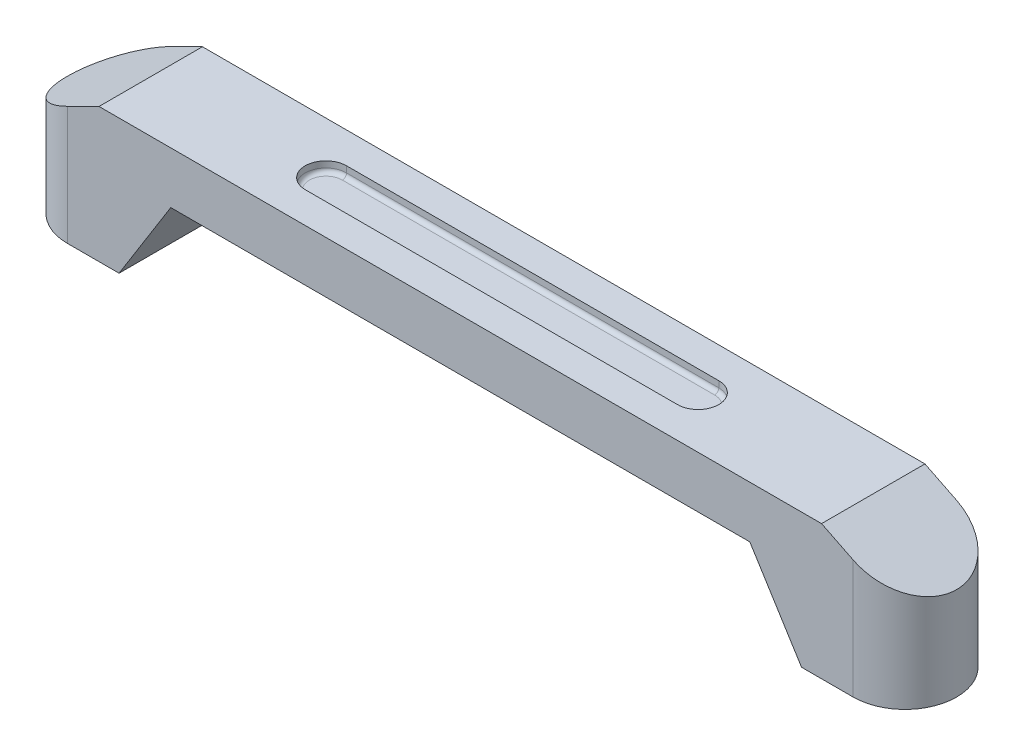
SolidWorks part; units mm, degrees
ref_plane "前视基准面" through (0, 0, 0) normal (0, 0, 1) x (1, 0, 0)
ref_plane "上视基准面" through (0, 0, 0) normal (0, 1, 0) x (1, 0, 0)
ref_plane "右视基准面" through (0, 0, 0) normal (1, 0, 0) x (0, 0, -1)
sketch "草图1" plane through (0, 0, 0) normal (0, 1, 0) x (1, 0, 0)
  line L0 (-19, 0) -> (19, 0) construction
  line L1 (-19, 2.5) -> (19, 2.5)
  line L2 (-19, -2.5) -> (19, -2.5)
  arc A0 (-19, 2.5) -> (-19, -2.5) centre (-19, 0) ccw
  arc A1 (19, -2.5) -> (19, 2.5) centre (19, 0) ccw
  point P2 (0, 0)
  point P8 (21.5, 0)
  point P9 (-21.5, 0)
  point P10 (-27.7653, 0)
  point P11 (27.9937, 0)
  point P12 (21.5, -2.5)
  point P13 (0, 0)
  point P14 (0, 0)
  point P15 (-21.4969, -0.1704)
  point P16 (0, 0)
  dimension "D1" = 5
  dimension "D2" = 43
extrude "凸台-拉伸1" add sketch "草图1" along normal blind 6.5
sketch "草图2" plane through (0, 0, 2.5) normal (0, 0, 1) x (1, 0, 0)
  line L0 (17.4689, 6.5) -> (21.5, 4.5)
  line L1 (-19, 6.5) -> (19, 6.5) construction
  line L2 (21.5, 0) -> (21.5, 6.5) construction
  line L3 (21.5, 4.5) -> (21.5, 7.4383)
  line L4 (21.5, 7.4383) -> (17.4689, 7.4383)
  line L5 (17.4689, 7.4383) -> (17.4689, 6.5)
  line L6 (19, 0) -> (21.5, 0) construction
  line L7 (0, 0) -> (0, -8.3353) construction
  line L8 (14, 4) -> (16.5, 0)
  line L9 (-14, 4) -> (14, 4)
  line L10 (-19, 0) -> (19, 0) construction
  line L11 (-21.5, 7.4383) -> (-17.4689, 7.4383)
  line L13 (-21.5, 4.5) -> (-21.5, 7.4383)
  line L14 (-17.4689, 6.5) -> (-21.5, 4.5)
  line L15 (-17.4689, 7.4383) -> (-17.4689, 6.5)
  line L16 (-14, 4) -> (-16.5, 0)
  line L17 (16.5, 0) -> (16.5, -3.0297)
  line L18 (16.5, -3.0297) -> (-16.5, -3.0297)
  line L19 (-16.5, -3.0297) -> (-16.5, 0)
  point P11 (0, 0)
  point P24 (0, 4)
  dimension "D1" = 4.5
  dimension "D2" = 4.5
  dimension "D3" = 14
  dimension "D4" = 16.5
  dimension "D5" = 4
extrude "切除-拉伸1" cut sketch "草图2" against normal up to next
sketch "草图3" plane through (0, 0, 0) normal (0, -1, 0) x (1, 0, 0)
  line L0 (0, 0) -> (0, -8.5718) construction
  line L1 (18.75, 0) -> (0, 0) construction
  circle A0 centre (18.75, 0) radius 1
  circle A1 centre (-18.75, 0) radius 1
  dimension "D1" = 2
  dimension "D2" = 18.75
extrude "切除-拉伸2" cut sketch "草图3" against normal blind 3.5
sketch "草图4" plane through (0, 6.5, 0) normal (0, 1, 0) x (1, 0, 0)
  line L0 (-9, 0) -> (9, 0) construction
  line L1 (-9, 1) -> (9, 1)
  line L2 (-9, -1) -> (9, -1)
  arc A0 (-9, 1) -> (-9, -1) centre (-9, 0) ccw
  arc A1 (9, -1) -> (9, 1) centre (9, 0) ccw
  point P2 (0, 0)
  point P8 (0, 0)
  point P10 (13.0247, 0)
  point P11 (-13.0247, 0)
  point P12 (10, 0)
  point P13 (0, 0)
  point P14 (0, 0)
  dimension "D1" = 18
  dimension "D2" = 2
extrude "切除-拉伸3" cut sketch "草图4" against normal blind 0.5
fillet "圆角1" radius 0.2 4 edges at (0, 6, -1) (10, 6, 0) (0, 6, 1) (-10, 6, 0)
